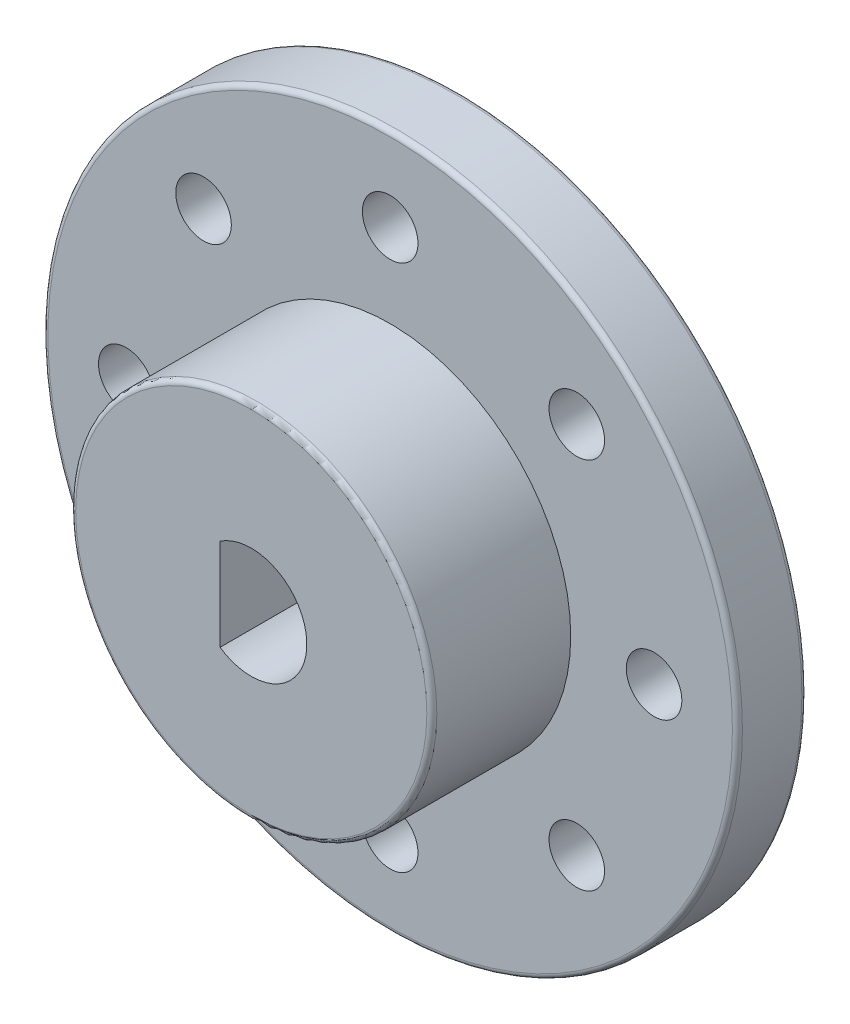
SolidWorks part; units mm, degrees
ref_plane "前视基准面" through (0, 0, 0) normal (0, 0, 1) x (1, 0, 0)
ref_plane "上视基准面" through (0, 0, 0) normal (0, 1, 0) x (1, 0, 0)
ref_plane "右视基准面" through (0, 0, 0) normal (1, 0, 0) x (0, 0, -1)
sketch "草图1" plane through (0, 0, 0) normal (0, 0, 1) x (1, 0, 0)
  circle A0 centre (0, 0) radius 25
  circle A1 centre (0, 0) radius 4
  dimension "D1" = 8
  dimension "D2" = 50
extrude "凸台-拉伸1" add sketch "草图1" along normal blind 5
sketch "草图2" plane through (0, 0, 5) normal (0, 0, 1) x (1, 0, 0)
  line L0 (3.7525, 0) -> (-2.2475, 0) construction
  line L1 (-2.2475, -3.3089) -> (-2.2475, 3.3089)
  arc A0 (-2.2475, 3.3089) -> (-2.2475, -3.3089) centre (0, 0) ccw
  dimension "D1" = 8
  dimension "D2" = 6
extrude "凸台-拉伸2" add sketch "草图2" against normal blind 5
sketch "草图5" plane through (0, 0, 5) normal (0, 0, 1) x (1, 0, 0)
  circle A0 centre (0, 0) radius 13
extrude "凸台-拉伸3" add sketch "草图5" along normal blind 10
sketch "草图6" plane through (0, 0, 0) normal (0, 0, -1) x (-1, 0, 0)
  line L0 (2.2475, 3.3089) -> (2.2475, -3.3089)
  arc A0 (2.2475, 3.3089) -> (2.2475, -3.3089) centre (0, 0) ccw
extrude "切除-拉伸1" cut sketch "草图6" against normal blind 18
sketch "草图7" plane through (0, 0, 5) normal (0, 0, 1) x (1, 0, 0)
  line L0 (0, 0) -> (-35.2333, 0) construction
  circle A0 centre (0, 19) radius 2
  circle A2 centre (13.435, 13.435) radius 2
  circle A3 centre (19, 0) radius 2
  circle A4 centre (13.435, -13.435) radius 2
  circle A5 centre (0, -19) radius 2
  circle A6 centre (-13.435, -13.435) radius 2
  circle A7 centre (-19, 0) radius 2
  circle A8 centre (-13.435, 13.435) radius 2
  point P25 (0, 0)
  dimension "D1" = 4
  dimension "D4" = 8
extrude "切除-拉伸2" cut sketch "草图7" against normal blind 18
fillet "圆角4" radius 0.36 3 edges at (25, 0, 5) (25, 0, 0) (13, 0, 15)
